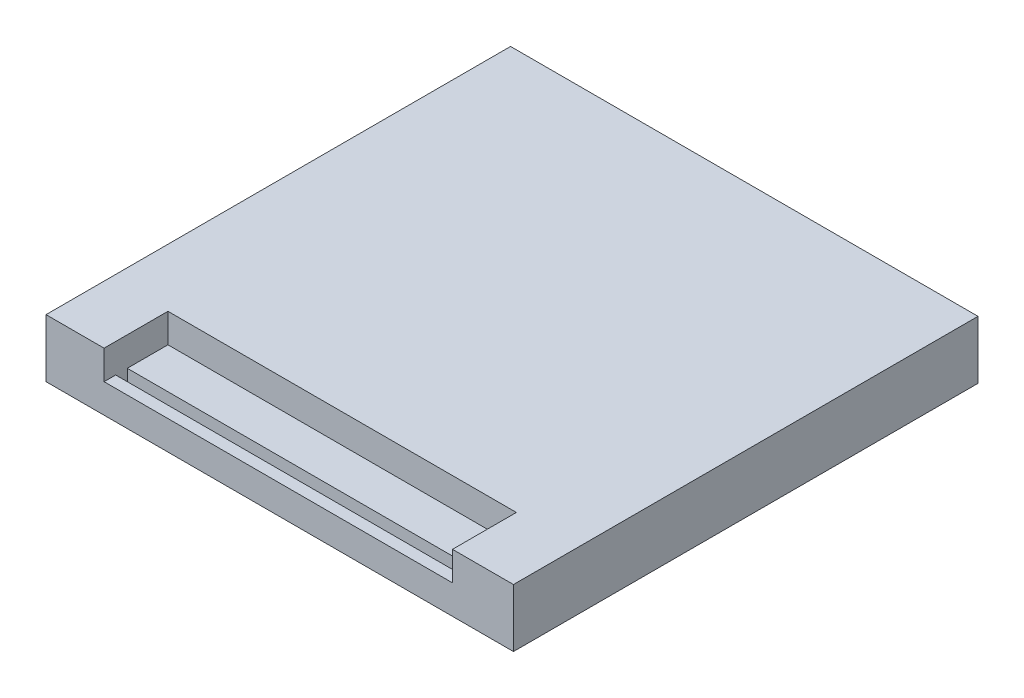
SolidWorks part; units mm, degrees
ref_plane "Front Plane" through (0, 0, 0) normal (0, 0, 1) x (1, 0, 0)
ref_plane "Top Plane" through (0, 0, 0) normal (0, 1, 0) x (1, 0, 0)
ref_plane "Right Plane" through (0, 0, 0) normal (1, 0, 0) x (0, 0, -1)
sketch "Sketch1" plane through (0, 0, 0) normal (0, 1, 0) x (1, 0, 0)
  line L1 (-40.25, 40) -> (40.25, 40)
  line L2 (-40.25, 40) -> (-40.25, -40)
  line L3 (-40.25, -40) -> (40.25, -40)
  line L4 (40.25, 40) -> (40.25, -40)
  line L5 (-40.25, 40) -> (40.25, -40) construction
  line L6 (-40.25, -40) -> (40.25, 40) construction
  point P0 (0, 0)
  dimension "D1" = 80
  dimension "D2" = 80.5
extrude "Boss-Extrude1" add sketch "Sketch1" along normal blind 10
sketch "Sketch2" plane through (-40.25, 0, 0) normal (-1, 0, 0) x (0, 0, 1)
  line L1 (40, 10) -> (29, 10)
  line L2 (40, 10) -> (40, 5)
  line L3 (40, 5) -> (29, 5)
  line L4 (29, 10) -> (29, 5)
  dimension "D1" = 5
  dimension "D2" = 11
extrude "Cut-Extrude1" cut sketch "Sketch2" against normal offset from surface (60 mm away) 70 from offset 10 up to face at (-40.25, 5, 0) offset against normal yes
sketch "Sketch3" plane through (-40.25, 0, 0) normal (-1, 0, 0) x (0, 0, 1)
  line L0 (29, 5) -> (40, 5) construction
  line L1 (38, 5) -> (36, 5)
  line L2 (38, 5) -> (38, 3)
  line L3 (38, 3) -> (36, 3)
  line L4 (36, 5) -> (36, 3)
  line L5 (40, 10) -> (40, 0) construction
  dimension "D1" = 2
  dimension "D2" = 2
  dimension "D3" = 2
extrude "Cut-Extrude2" cut sketch "Sketch3" against normal offset from surface (60 mm away) 70 from offset 10 up to face at (-40.25, 5, 0)
